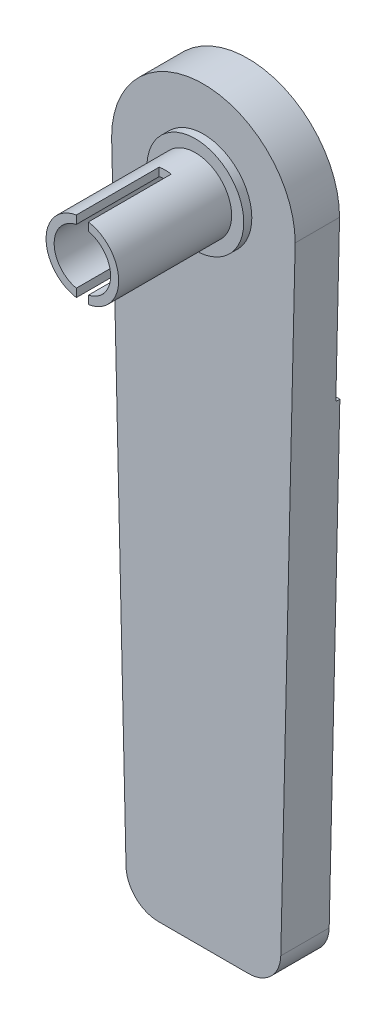
SolidWorks part; units mm, degrees
material "ABS"
ref_plane "前基準面" through (0, 0, 0) normal (0, 0, 1) x (1, 0, 0)
ref_plane "上基準面" through (0, 0, 0) normal (0, 1, 0) x (1, 0, 0)
ref_plane "右基準面" through (0, 0, 0) normal (1, 0, 0) x (0, 0, -1)
sketch "草圖1" plane through (0, 0, 0) normal (0, 0, 1) x (1, 0, 0)
  line L0 (0, 0) -> (0, -81.325) construction
  line L1 (0, 0) -> (0, 11.375) construction
  line L2 (-9.5, -81.325) -> (9.5, -81.325)
  line L8 (-9.5, -81.325) -> (-11.375, 0)
  line L9 (11.375, 0) -> (9.5, -81.325)
  arc A0 (11.3629, -0.5242) -> (-11.3629, -0.5242) centre (0, 0) ccw
  dimension "D1" = 92.7
  dimension "D2" = 22.75
  dimension "D3" = 19
extrude "填料-伸長1" add sketch "草圖1" along normal blind 6 contours L9 A0 L8 L2
fillet "圓角1" radius 4 2 edges at (9.5, -81.325, 3) (-9.5, -81.325, 3)
sketch "草圖2" plane through (0, 0, 6) normal (0, 0, 1) x (1, 0, 0)
  circle A0 centre (0, 0) radius 4.5
  dimension "D1" = 9
extrude "填料-伸長2" add sketch "草圖2" along normal blind 15
sketch "草圖4" plane through (0, 0, 6) normal (0, 0, 1) x (1, 0, 0)
  circle A0 centre (0, 0) radius 6
  dimension "D1" = 12
extrude "填料-伸長3" add sketch "草圖4" along normal blind 1
sketch "草圖5" plane through (0, 0, 21) normal (0, 0, 1) x (1, 0, 0)
  circle A0 centre (0, 0) radius 3.5
  dimension "D1" = 7
extrude "除料-伸長1" cut sketch "草圖5" against normal blind 15
ref_plane "平面1" through (0, -4.5, 0) normal (0, -1, 0) x (-1, 0, 0)
sketch "草圖6" plane through (0, -4.5, 0) normal (0, -1, 0) x (-1, 0, 0)
  line L0 (-4.5, -21) -> (4.5, -21) construction
  line L1 (0.75, -21) -> (-0.75, -21)
  line L2 (0.75, -21) -> (0.75, -10.7337)
  line L3 (0.75, -10.7337) -> (-0.75, -10.7337)
  line L4 (-0.75, -21) -> (-0.75, -10.7337)
  point P6 (0.6381, -21)
  point P7 (3.2192, -21)
  point P8 (0, -21)
  dimension "D1" = 1.5
extrude "除料-伸長2" cut sketch "草圖6" against normal through all
sketch "草圖7" plane through (0, 0, 0) normal (0, 0, -1) x (-1, 0, 0)
  line L0 (-10.9139, -20) -> (10.9139, -20)
  line L3 (-11.375, 0) -> (-9.5901, -77.4172)
  line L4 (-5.5912, -81.325) -> (5.5912, -81.325)
  line L5 (9.5901, -77.4172) -> (11.375, 0)
  line L6 (-11.375, 0) -> (-10.9139, -20)
  line L8 (10.9139, -20) -> (11.375, 0)
  arc A3 (-9.5901, -77.4172) -> (-5.5912, -81.325) centre (-5.5912, -77.325) ccw
  arc A4 (5.5912, -81.325) -> (9.5901, -77.4172) centre (5.5912, -77.325) ccw
  arc A5 (11.375, 0) -> (-11.375, 0) centre (0, 0) ccw
  arc A8 (11.375, 0) -> (-11.375, 0) centre (0, 0) ccw
  dimension "D2" = 20
  dimension "D1" = 0
extrude "除料-伸長3" cut sketch "草圖7" against normal blind 0.5
